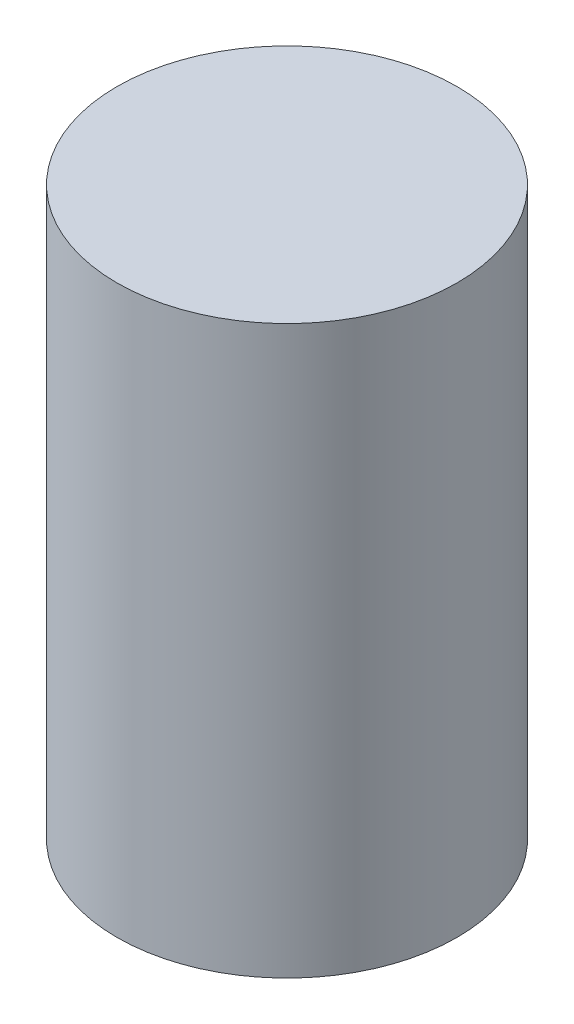
SolidWorks part; units mm, degrees
material "Epoxy, Unfilled"
ref_plane "Front Plane" through (0, 0, 0) normal (0, 0, 1) x (1, 0, 0)
ref_plane "Top Plane" through (0, 0, 0) normal (0, 1, 0) x (1, 0, 0)
ref_plane "Right Plane" through (0, 0, 0) normal (1, 0, 0) x (0, 0, -1)
sketch "Sketch2" plane through (0, 0, 0) normal (0, 1, 0) x (1, 0, 0)
  circle A0 centre (0, 0) radius 22.5
  dimension "D1" = 45
extrude "Boss-Extrude1" add sketch "Sketch2" along normal blind 75
sketch "Sketch7" plane through (0, 0, 0) normal (1, 0, 0) x (0, 0, -1)
  line L0 (0, 75) -> (0, 80.6637)
  line L1 (22.5, 75) -> (-22.5, 75) construction
  line L2 (0, 80.6637) -> (0.2068, 80.6637)
  arc A0 (0, 80.6637) -> (4.0032, 89.8737) centre (12.5958, 80.6637) cw
